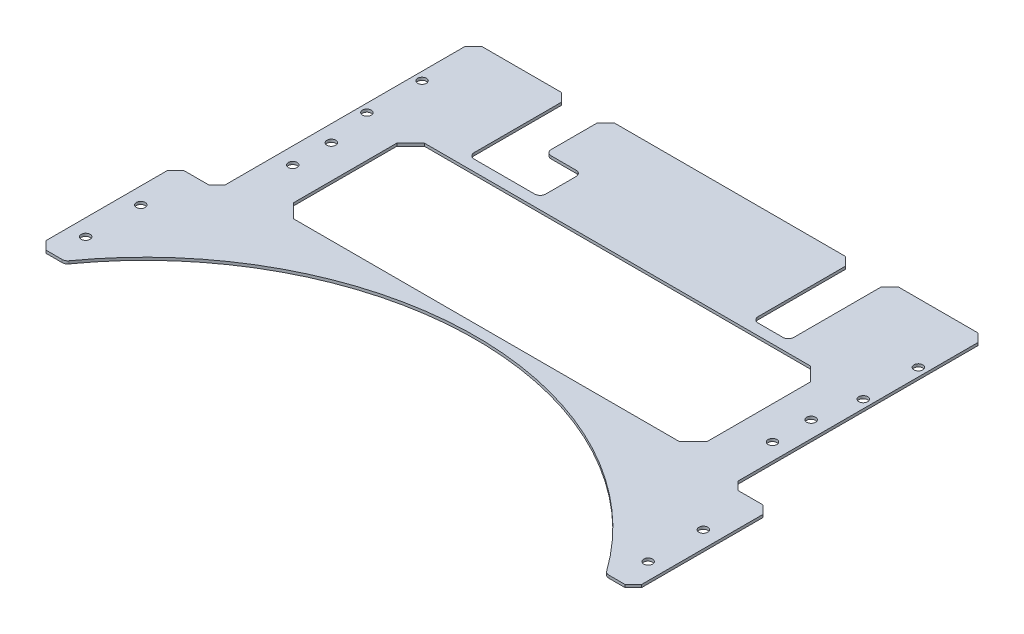
SolidWorks part; units mm, degrees
material "Hexcel AS4C (3000 丝)"
ref_plane "前视基准面" through (0, 0, 0) normal (0, 0, 1) x (1, 0, 0)
ref_plane "上视基准面" through (0, 0, 0) normal (0, 1, 0) x (1, 0, 0)
ref_plane "右视基准面" through (0, 0, 0) normal (1, 0, 0) x (0, 0, -1)
sketch "草图1" plane through (0, 0, 0) normal (0, 1, 0) x (1, 0, 0)
  line L1 (-93, 55) -> (93, 55)
  line L2 (-93, 55) -> (-93, -55)
  line L3 (-93, -55) -> (93, -55)
  line L4 (93, 55) -> (93, -55)
  line L5 (0, -55) -> (0, 55) construction
  line L6 (-93, 0) -> (93, 0) construction
  point P0 (0, 0)
  dimension "D1" = 186
  dimension "D2" = 110
extrude "凸台-拉伸1" add sketch "草图1" along normal blind 1
sketch "草图2" plane through (0, 1, 0) normal (0, 1, 0) x (1, 0, 0)
  line L0 (0, -55) -> (0, -50055) construction
  line L1 (-93, -55) -> (93, -55) construction
  line L2 (90, 55) -> (90, -49945) construction
  line L4 (93, -55) -> (93, 55) construction
  circle A0 centre (90, 15.38) radius 1.6
  circle A1 centre (90, 35.38) radius 1.6
  circle A2 centre (-90, 35.38) radius 1.6
  circle A3 centre (-90, 15.38) radius 1.6
  point P4 (0, -55)
  dimension "D2" = 20
  dimension "3.2" = 3.2
  dimension "D1" = 3
  dimension "D3" = 70.38
extrude "切除-拉伸1" cut sketch "草图2" against normal through all
sketch "草图3" plane through (0, 1, 0) normal (0, 1, 0) x (1, 0, 0)
  line L0 (0, 55) -> (0, -49945) construction
  line L1 (93, 55) -> (-93, 55) construction
  circle A0 centre (0, -155.12) radius 120 construction
  point P4 (0, 55)
  dimension "D1" = 240
  dimension "D2" = 210.12
sketch "草图5" plane through (0, 1, 0) normal (0, 1, 0) x (1, 0, 0)
  line L0 (0, 55) -> (0, -49945) construction
  line L1 (93, 55) -> (-93, 55) construction
  line L2 (-108, -86) -> (108, -86)
  line L3 (-93, -36) -> (-108, -36)
  line L4 (-93, 55) -> (-93, -55) construction
  line L5 (-108, -36) -> (-108, -86)
  line L6 (-93, -36) -> (-93, -55)
  line L7 (-93, -55) -> (93, -55)
  line L8 (-93, -55) -> (93, -55) construction
  line L9 (93, -36) -> (93, -55)
  line L10 (108, -36) -> (108, -86)
  line L11 (93, -36) -> (108, -36)
  point P4 (0, 55)
  point P17 (0, -55)
  point P20 (0, -86)
  dimension "D1" = 15
  dimension "D2" = 50
  dimension "D3" = 19
extrude "凸台-拉伸2" add sketch "草图5" against normal up to surface (1 mm away) up to face at (-90, 0, -16.98)
sketch "草图6" plane through (0, 1, 0) normal (0, 1, 0) x (1, 0, 0)
  circle A0 centre (0, -155.12) radius 120 construction
  circle A1 centre (0, -155.12) radius 120
extrude "切除-拉伸2" cut sketch "草图6" against normal through all
sketch "草图8" plane through (0, 1, 0) normal (0, 1, 0) x (1, 0, 0)
  line L0 (93, 55) -> (-93, 55)
  line L1 (93, 55) -> (93, 57)
  line L2 (-93, 55) -> (-93, 57)
  line L3 (93, 57) -> (-93, 57)
  dimension "D1" = 2
extrude "凸台-拉伸3" add sketch "草图8" against normal up to surface (1 mm away) up to face at (-90, 0, -16.98)
sketch "草图7" plane through (0, 1, 0) normal (0, 1, 0) x (1, 0, 0)
  line L0 (108, -36) -> (93, -36) construction
  line L1 (0, 57) -> (0, 50057) construction
  line L2 (93, 57) -> (-93, 57) construction
  line L3 (108, -86) -> (108, -36) construction
  circle A0 centre (47.5, 46.38) radius 1.25 construction
  circle A1 centre (47.5, 53.88) radius 1.25 construction
  circle A4 centre (47.5, 46.38) radius 1.25
  circle A5 centre (47.5, 53.88) radius 1.25
  circle A6 centre (102, -74.62) radius 1.6
  circle A7 centre (102, -54.62) radius 1.6
  circle A8 centre (-102, -54.62) radius 1.6
  circle A9 centre (-102, -74.62) radius 1.6
  circle A10 centre (-47.5, 53.88) radius 1.25
  circle A11 centre (-47.5, 46.38) radius 1.25
  point P19 (0, 57)
  dimension "D1" = 3.2
  dimension "D2" = 18.62
  dimension "D3" = 6
  dimension "D4" = 20
extrude "切除-拉伸3" cut sketch "草图7" against normal through all
sketch "草图9" plane through (0, 1, 0) normal (0, 1, 0) x (1, 0, 0)
  line L1 (55, 52.23) -> (55, 20.23)
  line L2 (40, 52.23) -> (40, 20.23)
  line L3 (55, 20.23) -> (40, 20.23)
  line L4 (52, 69.7646) -> (43, 69.7646)
  line L5 (40, 66.7646) -> (40, 52.23)
  line L6 (40, 52.23) -> (55, 52.23)
  line L7 (55, 52.23) -> (55, 66.7646)
  line L8 (52, 69.7646) -> (43, 69.7646)
  line L9 (0, 57) -> (0, 49160.3441) construction
  line L10 (93, 57) -> (-93, 57) construction
  line L12 (-40, 66.7646) -> (-40, 52.23)
  line L13 (-52, 69.7646) -> (-43, 69.7646)
  line L14 (-55, 52.23) -> (-55, 66.7646)
  line L15 (-55, 52.23) -> (-55, 20.23)
  line L16 (-55, 20.23) -> (-40, 20.23)
  line L17 (-40, 52.23) -> (-40, 20.23)
  line L27 (40, 66.7646) -> (40, 52.23)
  line L29 (55, 52.23) -> (55, 66.7646)
  arc A0 (-43, 69.7646) -> (-40, 66.7646) centre (-43, 66.7646) cw
  arc A1 (-55, 66.7646) -> (-52, 69.7646) centre (-52, 66.7646) cw
  arc A4 (43, 69.7646) -> (40, 66.7646) centre (43, 66.7646) ccw
  arc A5 (55, 66.7646) -> (52, 69.7646) centre (52, 66.7646) ccw
  arc A6 (43, 69.7646) -> (40, 66.7646) centre (43, 66.7646) ccw
  arc A7 (55, 66.7646) -> (52, 69.7646) centre (52, 66.7646) ccw
  point P8 (0, 57)
  dimension "D1" = 32
  dimension "D2" = 0
extrude "切除-拉伸4" cut sketch "草图9" against normal through all
sketch "草图10" plane through (0, 1, 0) normal (0, 1, 0) x (1, 0, 0)
  line L1 (-40, 20.23) -> (-32, 20.23)
  line L2 (-40, 20.23) -> (-40, 35.23)
  line L3 (-40, 35.23) -> (-32, 35.23)
  line L4 (-32, 20.23) -> (-32, 35.23)
  line L5 (-36, 35.23) -> (-36, 20.23) construction
  line L6 (-40, 27.73) -> (-32, 27.73) construction
  point P128 (-36, 27.73)
  dimension "D1" = 15
  dimension "10" = 8
extrude "切除-拉伸5" cut sketch "草图10" against normal through all
sketch "草图11" plane through (0, 1, 0) normal (0, 1, 0) x (1, 0, 0)
  line L0 (93, 95.1844) -> (-93, 95.1844) construction
  line L1 (75, 16.23) -> (-75, 16.23)
  line L2 (75, 16.23) -> (75, -31.27)
  line L3 (75, -31.27) -> (-75, -31.27)
  line L4 (-75, 16.23) -> (-75, -31.27)
  line L5 (93, -36) -> (93, 57) construction
  line L6 (-93, 57) -> (-93, -36) construction
  line L7 (0, 95.1844) -> (0, -164.1563) construction
  line L8 (-55, 20.23) -> (-32, 20.23) construction
  dimension "D1" = 150
  dimension "D2" = 47.5
  dimension "D3" = 4
extrude "切除-拉伸6" cut sketch "草图11" against normal through all
chamfer "倒角2" distance 5 angle 45 4 edges at (-75, 0.5, 31.27) (-75, 0.5, -16.23) (75, 0.5, 31.27) (75, 0.5, -16.23)
sketch "草图12" plane through (0, 1, 0) normal (0, 1, 0) x (1, 0, 0)
  line L0 (-75, -7.52) -> (-115.5568, -7.52) construction
  line L1 (-75, 11.23) -> (-75, -26.27) construction
  line L2 (93, 205.67) -> (-93, 205.67) construction
  line L3 (93, -36) -> (93, 57) construction
  line L4 (-93, 57) -> (-93, -36) construction
  line L5 (0, 205.67) -> (0, -229.0955) construction
  circle A0 centre (-87, -0.52) radius 1.6
  circle A1 centre (-87, -14.52) radius 1.6
  circle A2 centre (87, -14.52) radius 1.6
  circle A3 centre (87, -0.52) radius 1.6
  dimension "D2" = 3.2
  dimension "D1" = 12
  dimension "D3" = 7
extrude "切除-拉伸7" cut sketch "草图12" against normal through all
sketch "草图13" plane through (0, 1, 0) normal (0, 1, 0) x (1, 0, 0)
  line L0 (38.2458, 9.5825) -> (-50.768, 9.5825) construction
  line L1 (41.5483, -29.0318) -> (41.5483, 6.282) construction
  line L2 (-54.2733, 6.2894) -> (-54.2733, -29.0412) construction
  line L3 (-50.7755, -32.5391) -> (38.2552, -32.5391) construction
  line L4 (38.2458, 9.5825) -> (-50.768, 9.5825)
  line L5 (41.5483, -29.0318) -> (41.5483, 6.282)
  line L6 (-54.2733, 6.2894) -> (-54.2733, -29.0412)
  line L7 (-50.7755, -32.5391) -> (38.2552, -32.5391)
  spline S0 degree 3 poles (6036.0583, 21121.5233) (530.9883, -317.0349) (-68.3585, -27.5459) (-53.6516, 7.9423) (-53.4069, 8.3085) (-52.7961, 8.9197) (-52.43, 9.1646) (-17.0805, 23.8356) (270.9203, -570.6352) (-21178.6635, -6040.3658) knots -21.737156 -21.737156 -21.737156 -21.737156 0.25 0.25 0.5 0.5 0.75 0.75 22.65205 22.65205 22.65205 22.65205 only from (-54.0685, 6.28) to (-50.768, 9.5825) construction
  spline S1 degree 3 poles (21153.4891, -6080.5443) (-285.0692, -575.4744) (4.4198, 23.8725) (39.908, 9.1655) (40.2743, 8.9208) (40.8855, 8.31) (41.1303, 7.9439) (55.8014, -27.4056) (-538.6694, -315.4063) (-6008.4001, 21134.1774) knots -21.737156 -21.737156 -21.737156 -21.737156 0.25 0.25 0.5 0.5 0.75 0.75 22.65205 22.65205 22.65205 22.65205 only from (38.2458, 9.5825) to (41.5483, 6.282) construction
  spline S2 degree 3 poles (-6048.5781, -21144.2759) (-543.5086, 294.2831) (55.8382, 4.7941) (41.1313, -30.6941) (40.8866, -31.0604) (40.2758, -31.6715) (39.9097, -31.9164) (4.5602, -46.5874) (-283.4406, 547.8834) (21166.1437, 6017.6148) knots -21.737156 -21.737156 -21.737156 -21.737156 0.25 0.25 0.5 0.5 0.75 0.75 22.65205 22.65205 22.65205 22.65205 only from (41.5483, -29.0318) to (38.2477, -32.3343) construction
  spline S3 degree 3 poles (-21166.0093, 6057.7925) (272.5489, 552.7225) (-16.9401, -46.6243) (-52.4283, -31.9173) (-52.7946, -31.6726) (-53.4057, -31.0618) (-53.6506, -30.6958) (-68.3217, 4.6538) (526.1491, 292.6545) (5995.8798, -21156.9293) knots -21.737156 -21.737156 -21.737156 -21.737156 0.25 0.25 0.5 0.5 0.75 0.75 22.65205 22.65205 22.65205 22.65205 only from (-50.766, -32.3343) to (-54.0685, -29.0338) construction
  spline S4 degree 3 poles (-54.0685, 6.28) (-54.0682, 6.7124) (-53.9822, 7.1443) (-53.6516, 7.9423) (-53.4069, 8.3085) (-52.7961, 8.9197) (-52.43, 9.1646) (-51.6321, 9.4957) (-51.2002, 9.5819) (-50.768, 9.5825) knots 0 0 0 0 0.25 0.25 0.5 0.5 0.75 0.75 1 1 1 1
  spline S5 degree 3 poles (38.2458, 9.5825) (38.6782, 9.5822) (39.1101, 9.4962) (39.908, 9.1655) (40.2743, 8.9208) (40.8855, 8.31) (41.1303, 7.9439) (41.4615, 7.1461) (41.5477, 6.7141) (41.5483, 6.282) knots 0 0 0 0 0.25 0.25 0.5 0.5 0.75 0.75 1 1 1 1
  spline S6 degree 3 poles (41.5483, -29.0318) (41.548, -29.4643) (41.462, -29.8961) (41.1313, -30.6941) (40.8866, -31.0604) (40.2758, -31.6715) (39.9097, -31.9164) (39.1118, -32.2475) (38.6799, -32.3338) (38.2477, -32.3343) knots 0 0 0 0 0.25 0.25 0.5 0.5 0.75 0.75 1 1 1 1
  spline S7 degree 3 poles (-50.766, -32.3343) (-51.1985, -32.334) (-51.6303, -32.248) (-52.4283, -31.9173) (-52.7946, -31.6726) (-53.4057, -31.0618) (-53.6506, -30.6958) (-53.9818, -29.8979) (-54.068, -29.466) (-54.0685, -29.0338) knots 0 0 0 0 0.25 0.25 0.5 0.5 0.75 0.75 1 1 1 1
sketch "草图14" plane through (0, 1, 0) normal (0, 1, 0) x (1, 0, 0)
  line L0 (-55, 57) -> (-93, 57) construction
  line L1 (0, 57) -> (0, -45893.8781) construction
  line L2 (-55, 20.23) -> (-58, 20.23)
  line L3 (-55, 20.23) -> (-55, 57)
  line L4 (-55, 57) -> (-58, 57)
  line L5 (-58, 20.23) -> (-58, 57)
  line L6 (-56.5, 57) -> (-56.5, 20.23) construction
  line L7 (-55, 38.615) -> (-58, 38.615) construction
  line L8 (40, 57) -> (-40, 57) construction
  line L10 (55, 57) -> (58, 57)
  line L11 (58, 20.23) -> (58, 57)
  line L12 (55, 20.23) -> (58, 20.23)
  line L13 (55, 20.23) -> (55, 57)
  point P10 (0, 57)
  point P201 (-56.5, 38.615)
  dimension "D1" = 3
extrude "切除-拉伸8" cut sketch "草图14" against normal through all and the other way through all
sketch "草图15" plane through (0, 1, 0) normal (0, 1, 0) x (1, 0, 0)
  line L0 (0, 57) -> (0, -29465.7713) construction
  line L1 (40, 57) -> (-40, 57) construction
  line L3 (-58, 20.23) -> (-32, 20.23) construction
  line L4 (40, 20.23) -> (45, 20.23)
  line L5 (-40, 57) -> (-45, 57)
  line L6 (-40, 57) -> (-40, 20.23)
  line L7 (-40, 20.23) -> (-45, 20.23)
  line L8 (-45, 57) -> (-45, 20.23)
  line L9 (-42.5, 20.23) -> (-42.5, 57) construction
  line L10 (-40, 38.615) -> (-45, 38.615) construction
  line L11 (45, 57) -> (45, 20.23)
  line L12 (40, 57) -> (45, 57)
  line L13 (40, 57) -> (40, 20.23)
  point P4 (0, 57)
  point P282 (-42.5, 38.615)
  dimension "D1" = 5
extrude "凸台-拉伸4" add sketch "草图15" against normal up to surface (1 mm away) up to face at (87, 0, -1.08)
sketch "草图16" plane through (0, 1, 0) normal (0, 1, 0) x (1, 0, 0)
  line L2 (-45, 20.23) -> (-39, 20.23)
  line L3 (-45, 20.23) -> (-45, 35.23)
  line L4 (-45, 35.23) -> (-39, 35.23)
  line L5 (-39, 20.23) -> (-39, 35.23)
  line L6 (-42, 35.23) -> (-42, 20.23) construction
  line L7 (-45, 27.73) -> (-39, 27.73) construction
  point P277 (-42, 27.73)
  dimension "D1" = 6
  dimension "D2" = 15
extrude "切除-拉伸9" cut sketch "草图16" against normal through all
chamfer "倒角1" distance 3 angle 45 12 edges at (-93, 0.5, -57) (-93, 0.5, 36) (-108, 0.5, 36) (-108, 0.5, 86) (108, 0.5, 86) (108, 0.5, 36) (93, 0.5, 36) (93, 0.5, -57) (58, 0.5, -57) (45, 0.5, -57) (-45, 0.5, -57) (-58, 0.5, -57)
fillet "圆角1" radius 2 8 edges at (98.094, 0.5, 86) (-98.094, 0.5, 86) (-32, 0.5, -35.23) (-32, 0.5, -20.23) (58, 0.5, -20.23) (45, 0.5, -20.23) (-45, 0.5, -35.23) (-58, 0.5, -20.23)
fillet "圆角2" [suppressed] radius 1
